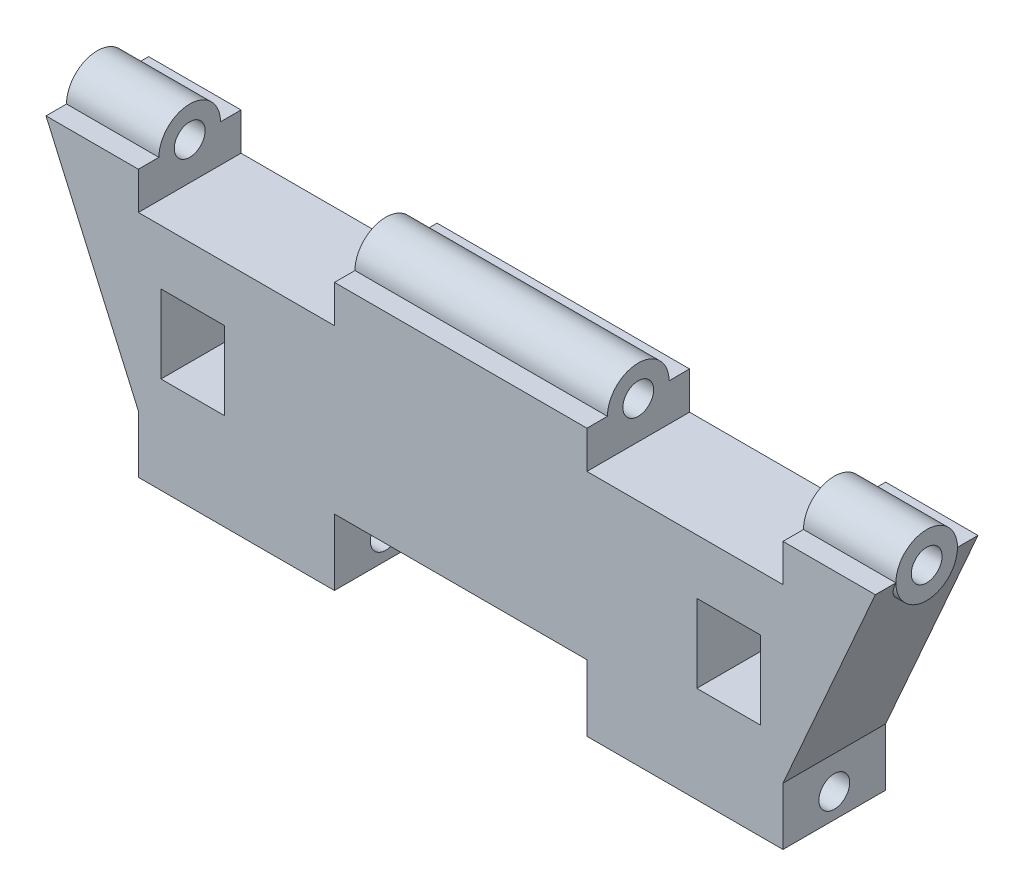
SolidWorks part; units mm, degrees
ref_plane "前视基准面" through (0, 0, 0) normal (0, 0, 1) x (1, 0, 0)
ref_plane "上视基准面" through (0, 0, 0) normal (0, 1, 0) x (1, 0, 0)
ref_plane "右视基准面" through (0, 0, 0) normal (1, 0, 0) x (0, 0, -1)
sketch "草图1" plane through (0, 0, 0) normal (0, 0, 1) x (1, 0, 0)
  line L0 (-20.2, 8) -> (20.2, 8)
  line L1 (-15.7, 5) -> (15.7, 5)
  line L2 (-15.7, 5) -> (-15.7, -5)
  line L3 (-15.7, -5) -> (15.7, -5)
  line L4 (15.7, 5) -> (15.7, -5)
  line L5 (0, -5) -> (0, 5) construction
  line L6 (-15.7, 0) -> (15.7, 0) construction
  line L7 (-15.7, 5) -> (-15.7, 8)
  line L8 (15.7, 5) -> (15.7, 8)
  line L9 (15.7, -5) -> (15.7, -2.2)
  line L10 (15.7, -2.2) -> (20.2, 8)
  line L11 (-15.7, -2.2) -> (-20.2, 8)
  point P0 (0, 0)
  point P7 (0, 5)
  point P15 (0, 8)
  dimension "D1" = 10
  dimension "D2" = 31.4
  dimension "D3" = 2.8
  dimension "D4" = 3
extrude "凸台-拉伸1" add sketch "草图1" along normal blind 5 contours L4 L1 L2 L3 | L1 L8 L0 L7 | L11 L2 L7 L0 | L4 L10 L0 L8
sketch "草图2" plane through (0, 0, 5) normal (0, 0, 1) x (1, 0, 0)
  line L0 (0, 10.2053) -> (0, -9.1495) construction
  line L2 (-14.6, 3.5) -> (-11.5, 3.5)
  line L3 (-14.6, 3.5) -> (-14.6, -0.3)
  line L4 (-14.6, -0.3) -> (-11.5, -0.3)
  line L5 (-11.5, 3.5) -> (-11.5, -0.3)
  line L9 (11.5, 3.5) -> (11.5, -0.3)
  line L10 (14.6, -0.3) -> (11.5, -0.3)
  line L11 (14.6, 3.5) -> (14.6, -0.3)
  line L12 (14.6, 3.5) -> (11.5, 3.5)
  line L13 (-20.2, 8) -> (20.2, 8) construction
  dimension "D1" = 3.8
  dimension "D2" = 3.1
  dimension "D3" = 23
  dimension "D4" = 4.5
extrude "切除-拉伸1" cut sketch "草图2" against normal through all
sketch "草图3" plane through (0, 0, 0) normal (1, 0, 0) x (0, 0, -1)
  line L0 (-5, 8) -> (0, 8) construction
  circle A0 centre (-2.5, 8) radius 1.5
  dimension "D1" = 3
extrude "凸台-拉伸2" add sketch "草图3" against normal up to vertex (20.2 mm away) and the other way up to vertex (20.2 mm away)
sketch "草图5" plane through (0, 0, 5) normal (0, 0, 1) x (1, 0, 0)
  line L0 (-20.2, 8) -> (20.2, 8) construction
  line L1 (-6.15, 9.8253) -> (-15.7, 9.8253)
  line L2 (-6.15, 9.8253) -> (-6.15, 6.1747)
  line L3 (-6.15, 6.1747) -> (-15.7, 6.1747)
  line L4 (-15.7, 9.8253) -> (-15.7, 6.1747)
  line L5 (-10.925, 6.1747) -> (-10.925, 9.8253) construction
  line L6 (-6.15, 8) -> (-15.7, 8) construction
  line L7 (0, 0) -> (0, 4.2576) construction
  line L8 (6.15, 8) -> (15.7, 8) construction
  line L9 (10.925, 6.1747) -> (10.925, 9.8253) construction
  line L10 (15.7, 9.8253) -> (15.7, 6.1747)
  line L11 (6.15, 6.1747) -> (15.7, 6.1747)
  line L12 (6.15, 9.8253) -> (6.15, 6.1747)
  line L13 (6.15, 9.8253) -> (15.7, 9.8253)
  line L14 (-20.2, 9.5) -> (-20.2, 8) construction
  line L15 (-15.7, -5) -> (15.7, -5) construction
  line L16 (-6.15, -8.2295) -> (6.15, -8.2295)
  line L17 (-6.15, -8.2295) -> (-6.15, -1.7705)
  line L18 (-6.15, -1.7705) -> (6.15, -1.7705)
  line L19 (6.15, -8.2295) -> (6.15, -1.7705)
  line L20 (0, -1.7705) -> (0, -8.2295) construction
  line L21 (-6.15, -5) -> (6.15, -5) construction
  point P0 (-10.925, 8)
  point P19 (10.925, 8)
  point P22 (0, -5)
  dimension "D1" = 12.3
  dimension "D2" = 4.5
extrude "切除-拉伸2" cut sketch "草图5" against normal blind 5
sketch "草图6" plane through (-20.2, 0, 0) normal (-1, 0, 0) x (0, 0, 1)
  circle A0 centre (2.5, 8) radius 0.75
  circle A1 centre (2.5, -3.8) radius 0.75
  dimension "D1" = 1.5
  dimension "D2" = 1.5
  dimension "D3" = 11.8
extrude "切除-拉伸3" cut sketch "草图6" against normal through all
